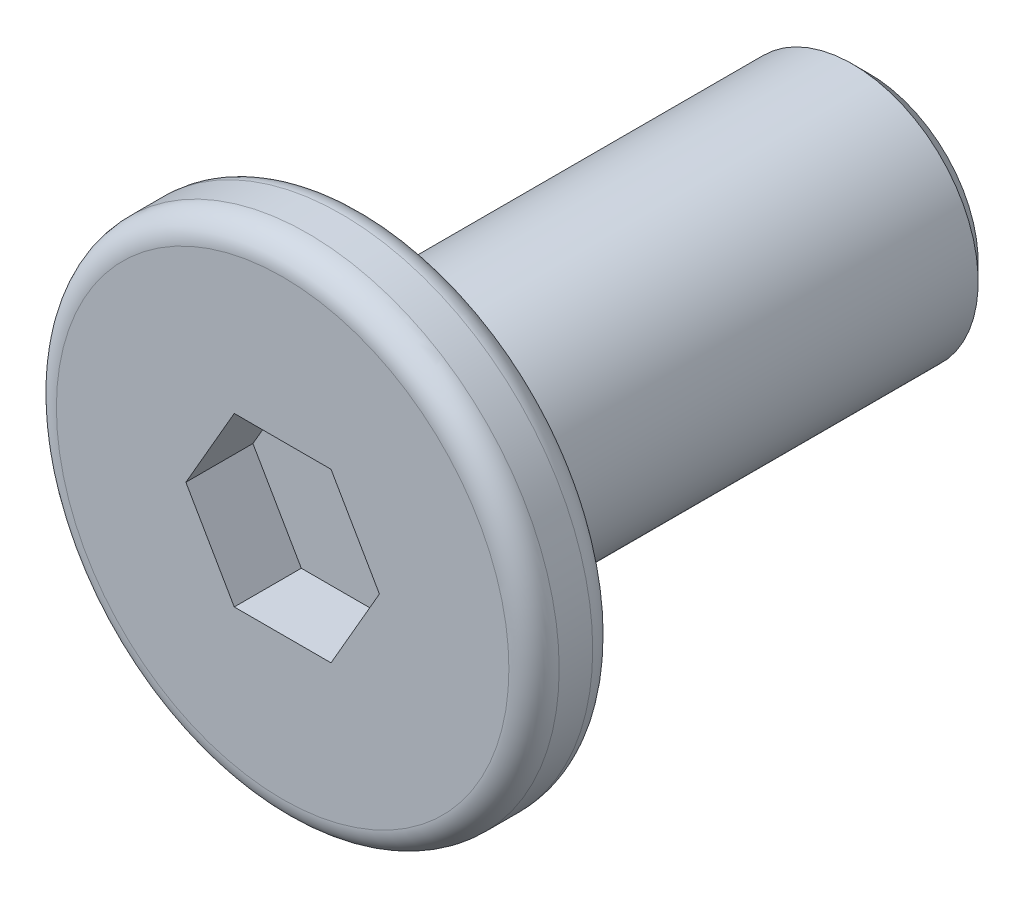
SolidWorks part; units mm, degrees
ref_plane "前视基准面" through (0, 0, 0) normal (0, 0, 1) x (1, 0, 0)
ref_plane "上视基准面" through (0, 0, 0) normal (0, 1, 0) x (1, 0, 0)
ref_plane "右视基准面" through (0, 0, 0) normal (1, 0, 0) x (0, 0, -1)
sketch "草图1" plane through (0, 0, 0) normal (0, 0, 1) x (1, 0, 0)
  circle A0 centre (0, 0) radius 3
  dimension "D1" = 6
extrude "凸台-拉伸1" add sketch "草图1" along normal mid plane 1
sketch "草图2" plane through (0, 0, -0.5) normal (0, 0, -1) x (-1, 0, 0)
  circle A0 centre (0, 0) radius 1.5
  dimension "D1" = 3
extrude "凸台-拉伸2" add sketch "草图2" along normal blind 6
chamfer "倒角1" distance 0.2 angle 45 1 edges at (-1.5, 0, -6.5)
sketch "草图3" plane through (0, 0, 0.5) normal (0, 0, 1) x (1, 0, 0)
  line L1 (1.1547, 0) -> (0.5774, 1)
  line L2 (0.5774, 1) -> (-0.5774, 1)
  line L3 (-0.5774, 1) -> (-1.1547, 0)
  line L4 (-1.1547, 0) -> (-0.5774, -1)
  line L5 (-0.5774, -1) -> (0.5774, -1)
  line L6 (0.5774, -1) -> (1.1547, 0)
  circle A0 centre (0, 0) radius 1 construction
  dimension "D1" = 2
extrude "切除-拉伸1" cut sketch "草图3" against normal blind 0.8
fillet "圆角2" radius 0.3 2 edges at (3, 0, -0.5) (3, 0, 0.5)
